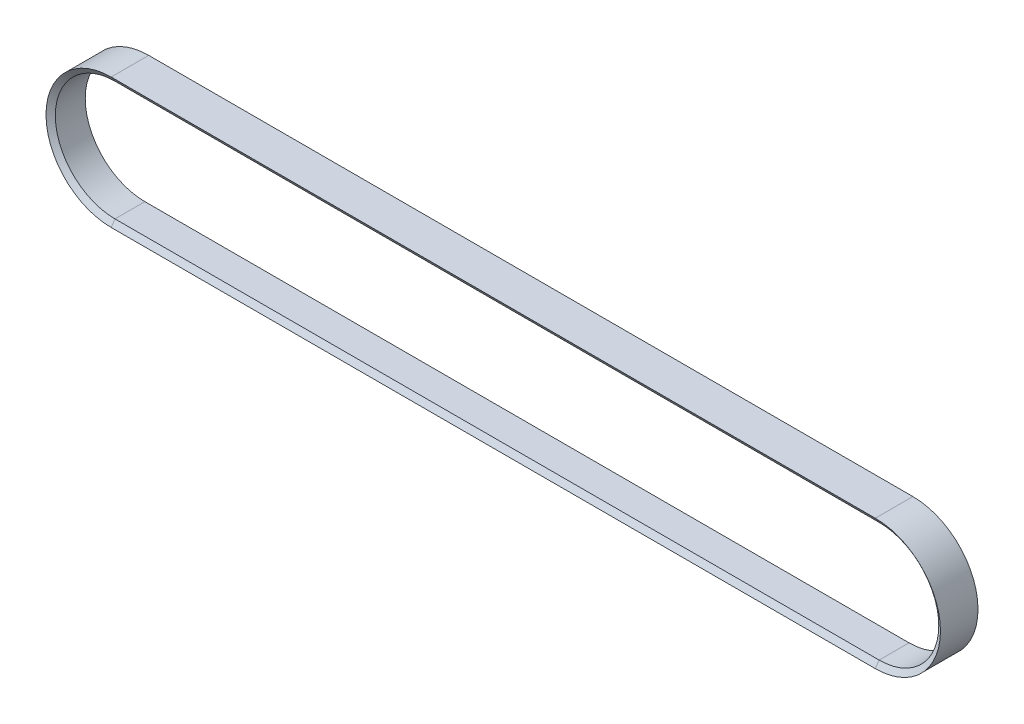
SolidWorks part; units mm, degrees
ref_plane "Front Plane" through (0, 0, 0) normal (0, 0, 1) x (1, 0, 0)
ref_plane "Top Plane" through (0, 0, 0) normal (0, 1, 0) x (1, 0, 0)
ref_plane "Right Plane" through (0, 0, 0) normal (1, 0, 0) x (0, 0, -1)
sketch "Sketch5" plane through (0, 0, 0) normal (0, 0, 1) x (1, 0, 0)
  line L0 (-54, 0) -> (746, 0) construction
  line L1 (692, 54) -> (0, 54)
  line L2 (0, -54) -> (692, -54)
  arc A0 (0, 54) -> (0, -54) centre (0, 0) ccw
  arc A1 (692, -54) -> (692, 54) centre (692, 0) ccw
  point P11 (0, 0)
  dimension "D1" = 108
  dimension "D2" = 108
  dimension "D3" = 800
sketch "Sketch6" plane through (0, 0, 0) normal (1, 0, 0) x (0, 0, -1)
  line L0 (-13.535, 54) -> (13.535, 54)
  line L1 (0, 54) -> (0, -54) construction
  line L2 (0, 54) -> (0, -54) construction
  line L3 (13.535, 54) -> (17, 59)
  line L4 (17, 59) -> (-17, 59)
  line L5 (0, 59) -> (0, 54) construction
  line L6 (-13.535, 54) -> (-17, 59)
  dimension "D1" = 5
  dimension "D2" = 13.535
  dimension "D3" = 17
sweep "Sweep2" add profiles "Sketch6" path "Sketch5"
